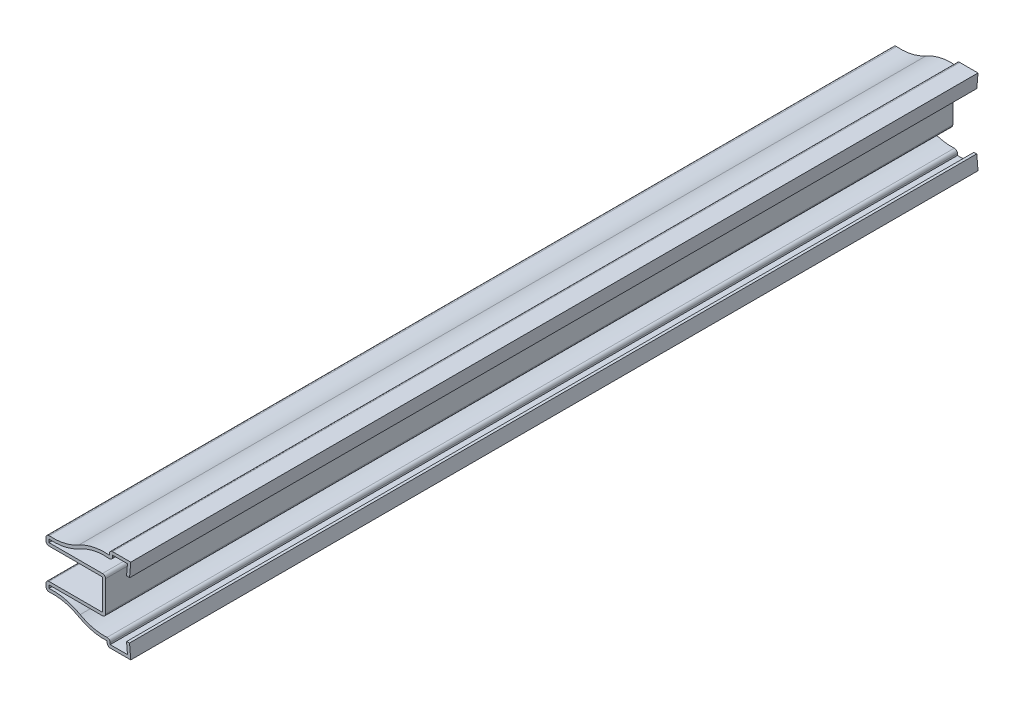
SolidWorks part; units mm, degrees
ref_plane "Front Plane" through (0, 0, 0) normal (0, 0, 1) x (1, 0, 0)
ref_plane "Top Plane" through (0, 0, 0) normal (0, 1, 0) x (1, 0, 0)
ref_plane "Right Plane" through (0, 0, 0) normal (1, 0, 0) x (0, 0, -1)
sketch "Sketch1" plane through (0, 0, 0) normal (0, 0, 1) x (1, 0, 0)
  line L0 (0, 0) -> (-9.525, 0) construction
  line L1 (-9.525, -5.1594) -> (-9.525, 5.1594)
  line L2 (-9.525, 5.1594) -> (-28.575, 5.1594)
  line L3 (-28.575, 5.1594) -> (-28.575, 8.3344)
  line L4 (-7.1437, 12.6691) -> (-7.1437, 14.2566)
  line L5 (-7.1437, 14.2566) -> (0, 14.2566)
  line L6 (0, 14.2566) -> (-0.3969, 9.4941)
  line L7 (0, -14.3184) -> (-0.3969, -9.5559)
  line L8 (-7.9375, -14.3184) -> (0, -14.3184)
  line L9 (-7.9375, -12.7309) -> (-7.9375, -14.3184)
  line L10 (-28.575, -5.1594) -> (-28.575, -8.3344)
  line L11 (-9.525, -5.1594) -> (-28.575, -5.1594)
  arc A0 (-28.575, 8.3344) -> (-17.5438, 10.4642) centre (-26.1937, 25.6338) ccw
  arc A1 (-17.5438, 10.4642) -> (-7.1437, 12.6691) centre (-8.8938, -4.7054) cw
  arc A2 (-17.5438, -10.4642) -> (-7.9375, -12.7309) centre (-8.8938, 4.7054) ccw
  arc A3 (-28.575, -8.3344) -> (-17.5438, -10.4642) centre (-26.1937, -25.6338) cw
  point P15 (-28.575, 6.7469)
  point P26 (-7.7409, -14.3471)
  dimension "D9" = 17.4625
  dimension "D1" = 28.575
  dimension "D2" = 0.3969
  dimension "D3" = 10.3187
  dimension "D4" = 19.05
  dimension "D5" = 7.1437
  dimension "D6" = 4.7625
  dimension "D7" = 3.175
  dimension "D8" = 1.5875
  dimension "D10" = 28.575
  dimension "D11" = 2.3813
  dimension "D12" = 7.9375
  dimension "D13" = 1.5875
  dimension "D14" = 4.7625
extrude "Extrude-Thin1" add sketch "Sketch1" against normal blind 285.75 thin
fillet "Fillet1" radius 1.016 10 edges at (-7.9375, -14.3184, -142.875) (-6.9215, -11.6224, -142.875) (-28.575, -8.3344, -142.875) (-28.575, -5.1594, -142.875) (-8.509, -6.1754, -142.875) (-8.509, 6.1754, -142.875) (-28.575, 5.1594, -142.875) (-28.575, 8.3344, -142.875) (-6.1277, 11.5068, -142.875) (-7.1437, 14.2566, -142.875)
